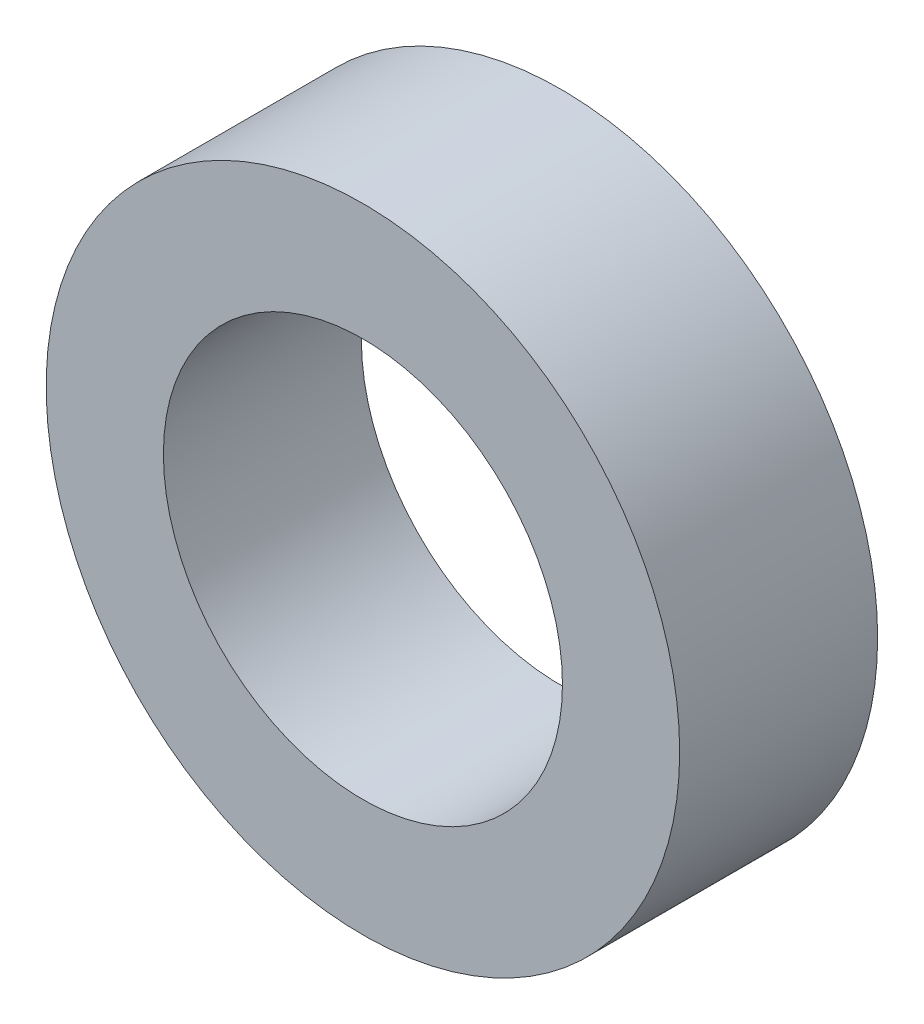
SolidWorks part; units mm, degrees
material "6061 Alloy"
ref_plane "Front Plane" through (0, 0, 0) normal (0, 0, 1) x (1, 0, 0)
ref_plane "Top Plane" through (0, 0, 0) normal (0, 1, 0) x (1, 0, 0)
ref_plane "Right Plane" through (0, 0, 0) normal (1, 0, 0) x (0, 0, -1)
sketch "Sketch1" plane through (0, 0, 0) normal (0, 0, 1) x (1, 0, 0)
  circle A0 centre (0, 0) radius 4
  circle A1 centre (0, 0) radius 6.35
  dimension "D1" = 8
  dimension "D2" = 12.7
extrude "Boss-Extrude1" add sketch "Sketch1" along normal blind 3.9688
